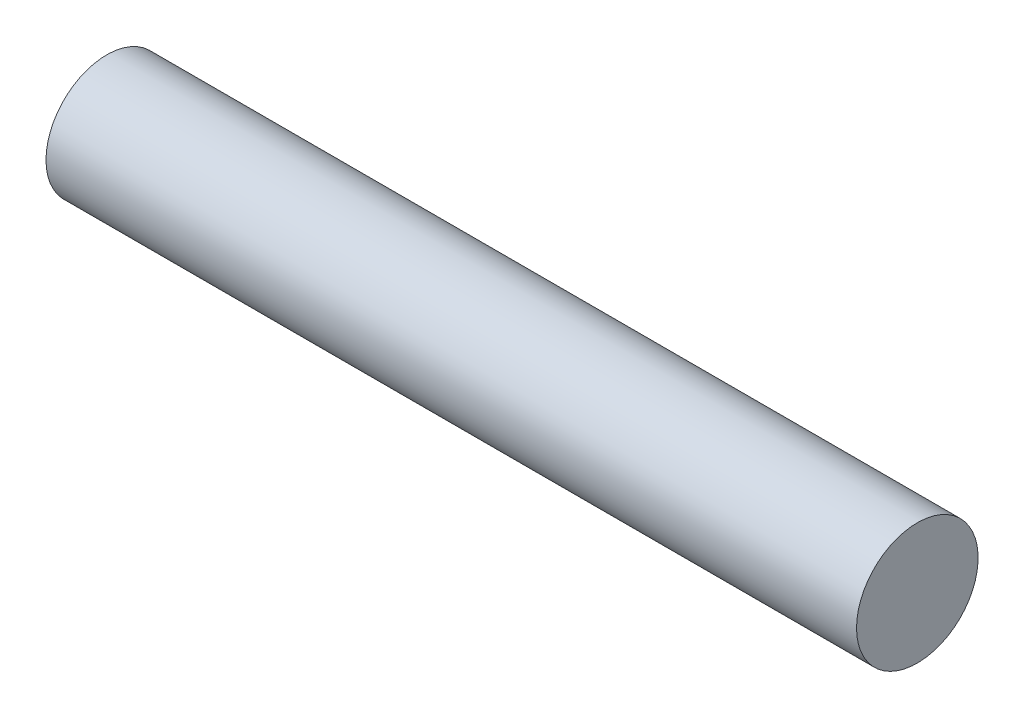
SolidWorks part; units mm, degrees
ref_plane "Front Plane" through (0, 0, 0) normal (0, 0, 1) x (1, 0, 0)
ref_plane "Top Plane" through (0, 0, 0) normal (0, 1, 0) x (1, 0, 0)
ref_plane "Right Plane" through (0, 0, 0) normal (1, 0, 0) x (0, 0, -1)
sketch "Sketch1" plane through (0, 0, 0) normal (0, 0, 1) x (1, 0, 0)
  line L0 (0, 0) -> (60, 0)
  dimension "D1" = 60
revolve "Revolve-Thin1" add sketch "Sketch1" angle 360 about L0 wall 4.5
